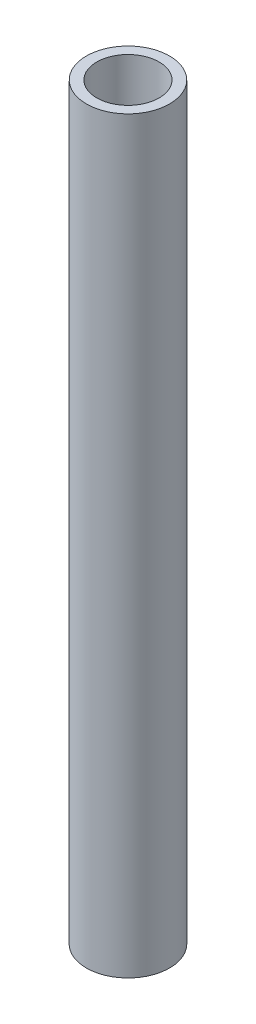
SolidWorks part; units mm, degrees
ref_plane "Front Plane" through (0, 0, 0) normal (0, 0, 1) x (1, 0, 0)
ref_plane "Top Plane" through (0, 0, 0) normal (0, 1, 0) x (1, 0, 0)
ref_plane "Right Plane" through (0, 0, 0) normal (1, 0, 0) x (0, 0, -1)
sketch "Sketch1" plane through (0, 0, 0) normal (0, 1, 0) x (1, 0, 0)
  circle A0 centre (-391.1817, 212.7433) radius 12.7
  circle A1 centre (-391.1817, 212.7433) radius 9.525
  dimension "D1" = 19.05
  dimension "D2" = 25.4
extrude "Boss-Extrude2" add sketch "Sketch1" along normal blind 228.6
